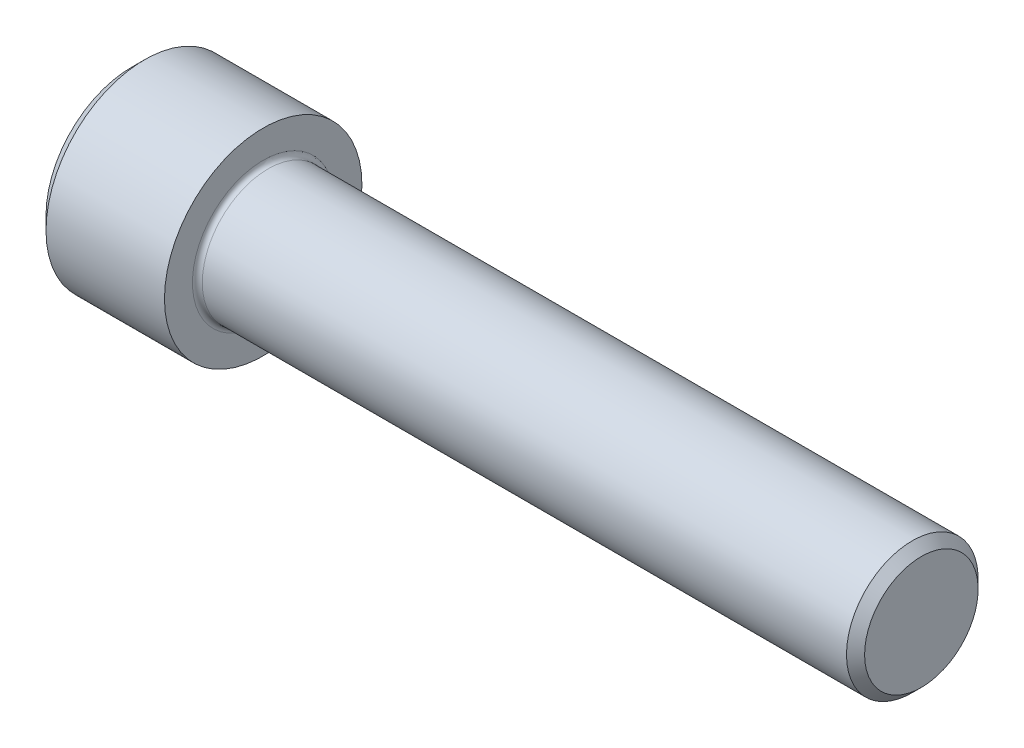
SolidWorks part; units mm, degrees
revolve "Base-Revolve" add sketch "BodySke"
sketch "BodySke" plane through (0, 0, 0) normal (0, 0, 1) x (1, 0, 0)
  line L0 (0, 0) -> (0, 10.4)
  line L1 (1.6, 12) -> (16, 12)
  line L2 (16, 12) -> (16, 8)
  line L3 (16, 8) -> (94.8985, 8)
  line L4 (96, 6.8985) -> (96, 0)
  line L5 (96, 0) -> (0, 0)
  line L6 (-31.75, 0) -> (127, 0) construction
  line L7 (0, 10.4) -> (1.6, 12)
  line L8 (96, 6.8985) -> (94.8985, 8)
  line L9 (0, -10.4) -> (1.6, -12) construction
  line L10 (96, -6.8985) -> (94.8985, -8) construction
  line L11 (18, 9.525) -> (18, 3.175) construction
  line L12 (52, 9.525) -> (52, 3.175) construction
  line L13 (46, 9.525) -> (46, 3.175) construction
  dimension "Diameter" = 16
  dimension "Head_ht" = 16
  dimension "Length" = 80
  dimension "Body_ch_ang" = 45
  dimension "Head_dia" = 24
  dimension "Head_ch_ang" = 45
  dimension "Minor_dia" = 13.797
  dimension "Advance" = 2
  dimension "Thread_nom" = 44
  dimension "Thread_length" = 50
  dimension "Head_ch_ht" = 1.6
cosmetic thread "ThreadCosmetic" [suppressed]
fillet "Fillet1" radius 0.6 1 edges at (16, 0, 8)
ref_plane "Plane1" through (0, 0, 0) normal (0, 0, 1) x (1, 0, 0)
ref_plane "Plane2" through (0, 0, 0) normal (0, 1, 0) x (1, 0, 0)
ref_plane "Plane3" through (0, 0, 0) normal (1, 0, 0) x (0, 0, -1)
sketch "Sketch2" plane through (0, 0, 0) normal (0, 0, 1) x (1, 0, 0)
  line L0 (0, 7.071) -> (8, 7.071)
  line L1 (8, 7.071) -> (12.0824, 0)
  line L2 (-31.75, 0) -> (127, 0) construction
  line L3 (12.0824, 0) -> (0, 0)
  line L4 (0, 0) -> (0, 7.071)
  line L5 (0, 10.4) -> (0, -10.4) construction
  line L6 (0, 0) -> (47.625, 0) construction
  line L7 (16, -12) -> (16, 12) construction
  dimension "D1" = 7.071
  dimension "D2" = 60
revolve "Hex-PreBroach" cut sketch "Sketch2" angle 360 about L6
sketch "Sketch3" plane through (0, 0, 0) normal (-1, 0, 0) x (0, 0.5, 0.866)
  line L0 (4.0824, 7.071) -> (-4.0824, 7.071)
  line L1 (-4.0824, 7.071) -> (-8.1649, 0)
  line L2 (4.0824, 7.071) -> (8.1649, 0)
  line L3 (4.0824, -7.071) -> (8.1649, 0)
  line L4 (4.0824, -7.071) -> (-4.0824, -7.071)
  line L5 (-4.0824, -7.071) -> (-8.1649, 0)
  dimension "D1" = 7.071
  dimension "D2" = 7.071
  dimension "Hex_size" = 14.142
extrude "Hex" cut sketch "Sketch3" against normal blind 8
sketch "Sketch4" plane through (0, 0, 0) normal (-1, 0, 0) x (0, 0, 1)
  line L0 (0, 0) -> (3.7846, 0)
  line L1 (0, 0) -> (6.1484, 3.5498) construction
  line L2 (0, 0) -> (1.8923, 3.2776)
  line L3 (3.1235, 0.8061) -> (3.6229, 1.0945)
  line L4 (2.2599, 2.3019) -> (2.7593, 2.5903)
  arc A0 (3.1235, 0.8061) -> (2.2599, 2.3019) centre (0, 0) ccw
  arc A1 (3.7846, 0) -> (3.6229, 1.0945) centre (0, 0) ccw
  arc A2 (1.8923, 3.2776) -> (2.7593, 2.5903) centre (0, 0) cw
  dimension "D1" = 30
  dimension "D2" = 60
  dimension "Spline_p_dim" = 1.7272
  dimension "D3" = 0.8636
extrude "Spline" [suppressed] cut sketch "Sketch4" against normal blind 8
pattern_circular "CirPattern1" [suppressed] count 6 every 60
sketch "Sketch5" plane through (0, 0, 0) normal (0, 0, 1) x (1, 0, 0)
  line L0 (-31.75, 0) -> (127, 0) construction
  line L2 (0, 10.4) -> (0, -10.4) construction
  circle A0 centre (5, 0) radius 0.825
  dimension "Drilled_hole_dia" = 1.65
  dimension "Drilled_hole_loc" = 5
extrude "Hole" [suppressed] cut sketch "Sketch5" against normal through all and the other way through all
pattern_circular "Drilled-4" [suppressed] count 2 every 60
pattern_circular "Drilled-6" [suppressed] count 3 every 60
sketch "ThdSchSke" plane through (0, 0, 0) normal (0, 0, 1) x (1, 0, 0)
  line L0 (52, -6.8985) -> (51.2287, -8)
  line L1 (52, -6.8985) -> (52.7713, -8)
  line L2 (52.7713, -8) -> (52.7713, -10)
  line L3 (-3.175, 0) -> (5.1513, 0) construction
  line L5 (52.7713, -10) -> (51.2287, -10)
  line L6 (51.2287, -10) -> (51.2287, -8)
  line L7 (0, 10.4) -> (0, -10.4) construction
  dimension "Thread_minor" = 13.797
  dimension "Diameter" = 16
  dimension "Start" = 52
revolve "ThreadSchematic" [suppressed] cut sketch "ThdSchSke" angle 360 about L3
pattern_linear "ThdSchPat" [suppressed]
equation "\"D2@Sketch3\" = \"Hex_size@Sketch3\" / 2"
equation "\"D1@Sketch3\" = \"Hex_size@Sketch3\" / 2"
equation "\"D1@Sketch2\" = \"Hex_size@Sketch3\" / 2"
equation "\"D3@Sketch4\" = \"Spline_p_dim@Sketch4\" / 2"
equation "\"Thread_minor@ThreadCosmetic\"  =  \"Minor_dia@BodySke\""
equation "\"D2@CirPattern1\" = 360 / \"Num_teeth@CirPattern1\""
equation "\"Wall_thickness@Sketch2\" = \"Head_ht@BodySke\" - \"Key_eng@Hex\""
equation "\"Thread_length@ThreadCosmetic\" = ((sgn( (\"Length@BodySke\" - \"Advance@BodySke\" ) - \"Thread_nom@BodySke\" )-1)*( (\"Length@BodySke\" - \"Advance@BodySke\" ) - \"Thread_nom@BodySke\" ))/-2+ \"Thread_nom@BodySke\""
equation "\"Thread_minor@ThdSchSke\" = \"Minor_dia@BodySke\""
equation "\"Diameter@ThdSchSke\" = \"Diameter@BodySke\""
equation "\"Overcut@ThdSchSke\" = \"Diameter@BodySke\" * 1.25"
equation "\"Start@ThdSchSke\" = \"Head_ht@BodySke\" + \"Length@BodySke\" - \"Thread_length@ThreadCosmetic\"  '---Non-countersunk---"
equation "\"Num_threads@ThdSchPat\" = int( \"Thread_length@ThreadCosmetic\" / \"Advance@BodySke\" + 0.999 )  + 1"
equation "\"Advance@ThdSchPat\" = \"Thread_length@ThreadCosmetic\" /  (\"Num_threads@ThdSchPat\" - 1) 'relax it"
equation "\"Num_threads@ThdSchPat\" = \"Num_threads@ThdSchPat\" - sgn( \"Num_threads@ThdSchPat\" - 1) '---chamfered tips only---"
